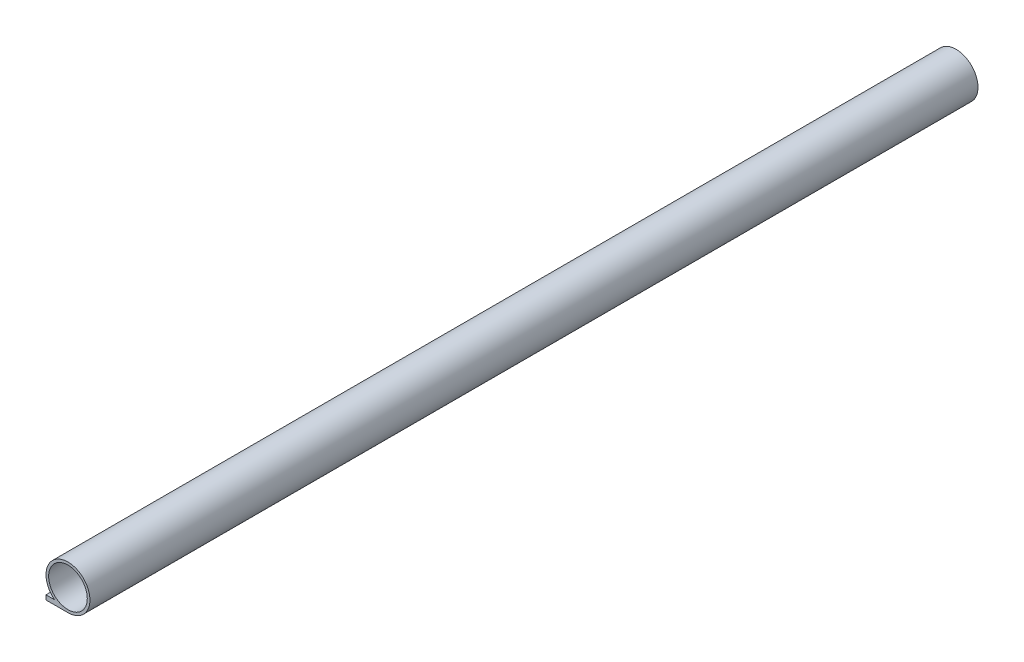
SolidWorks part; units mm, degrees
ref_plane "Front Plane" through (0, 0, 0) normal (0, 0, 1) x (1, 0, 0)
ref_plane "Top Plane" through (0, 0, 0) normal (0, 1, 0) x (1, 0, 0)
ref_plane "Right Plane" through (0, 0, 0) normal (1, 0, 0) x (0, 0, -1)
sketch "Sketch1" plane through (0, 0, 0) normal (0, 0, 1) x (1, 0, 0)
  line L3 (0, -12.7) -> (-12.7, -12.7)
  line L4 (-12.7, -12.7) -> (-12.7, -10.0965)
  line L5 (-12.7, -10.0965) -> (-7.7039, -10.0965)
  circle A0 centre (0, 0) radius 11.176
  arc A3 (0, -12.7) -> (-7.7039, -10.0965) centre (0, 0) ccw
  point P6 (0, 0)
  dimension "D1" = 25.4
  dimension "D2" = 22.352
  dimension "D3" = 12.7
  dimension "D4" = 2.6035
extrude "Boss-Extrude1" add sketch "Sketch1" along normal blind 513.588
sketch "Sketch2" plane through (-12.7, 0, 0) normal (-1, 0, 0) x (0, 0, 1)
  line L0 (0, -10.0965) -> (0, -12.7) construction
  line L1 (1.27, -10.6045) -> (512.318, -10.6045)
  line L2 (1.27, -10.6045) -> (1.27, -12.192)
  line L3 (1.27, -12.192) -> (512.318, -12.192)
  line L4 (512.318, -10.6045) -> (512.318, -12.192)
  line L5 (513.588, -10.0965) -> (0, -10.0965) construction
  line L6 (513.588, -10.0965) -> (513.588, -12.7) construction
  line L7 (513.588, -12.7) -> (0, -12.7) construction
  point P6 (0, -11.3983)
  dimension "D1" = 1.27
  dimension "D2" = 0.508
  dimension "D3" = 1.27
  dimension "D4" = 0.508
extrude "Cut-Extrude1" cut sketch "Sketch2" against normal blind 5.08
